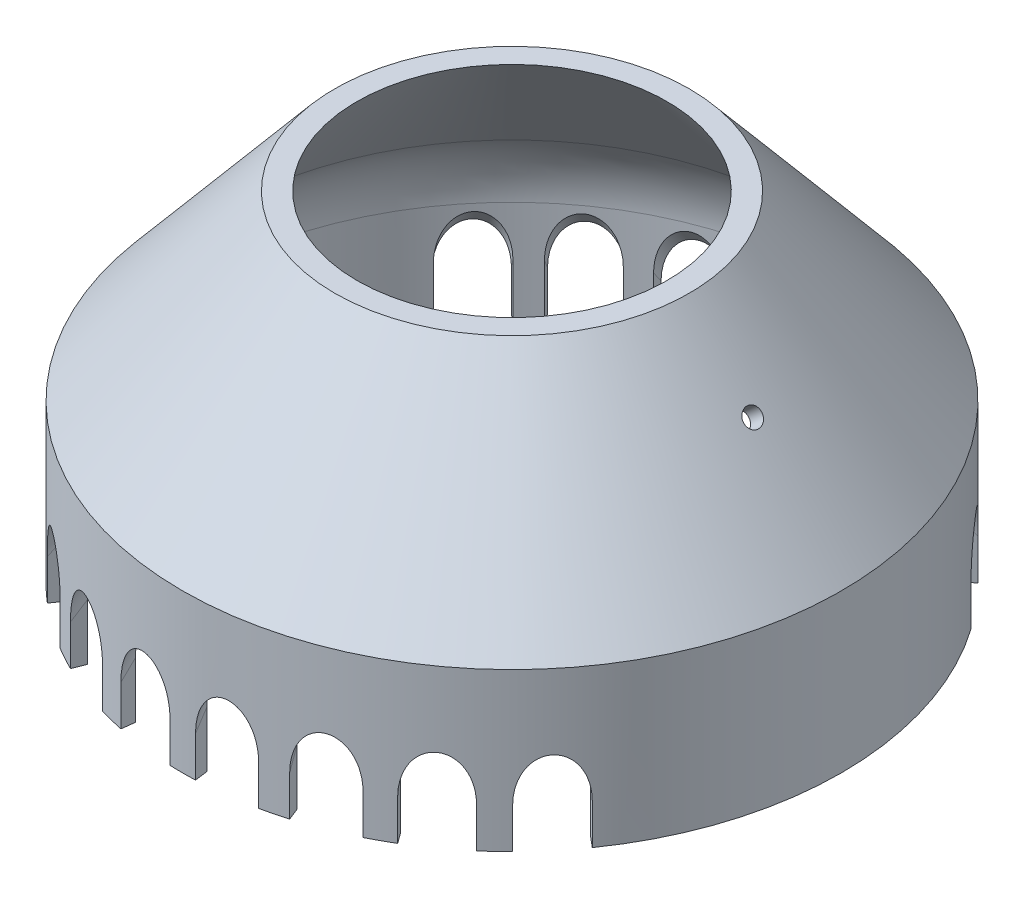
SolidWorks part; units mm, degrees
ref_plane "Front Plane" through (0, 0, 0) normal (0, 0, 1) x (1, 0, 0)
ref_plane "Top Plane" through (0, 0, 0) normal (0, 1, 0) x (1, 0, 0)
ref_plane "Right Plane" through (0, 0, 0) normal (1, 0, 0) x (0, 0, -1)
sketch "Cone Cross Section" plane through (0, 0, 0) normal (0, 0, -1) x (1, 0, 0)
  line L0 (0, 0) -> (13.7186, 0) construction
  line L1 (13.7186, 0) -> (25.6604, 14.2318)
  line L2 (28, 17.02) -> (29.1491, 16.0558) construction
  line L3 (13.7186, 0) -> (15.6767, 0)
  line L4 (29.1491, 16.0558) -> (15.6767, 0)
  line L5 (28, 20.6597) -> (28, 30)
  line L6 (0, 0) -> (0, 15.7221) construction
  line L7 (28, 30) -> (29.1491, 30)
  line L8 (29.1491, 30) -> (29.1491, 16.0558)
  arc A0 (25.6604, 14.2318) -> (28, 20.6597) centre (18, 20.6597) ccw
  dimension "D6" = 10
  dimension "D1" = 28
  dimension "D2" = 17.02
  dimension "D3" = 1.5
  dimension "D4" = 30
  dimension "D5" = 1.1491
  dimension "D7" = 13.9442
revolve "Revolve1" add sketch "Cone Cross Section" angle 360 about L6
sketch "Support Hole Plane Def Line" plane through (0, 0, 0) normal (0, 1, 0) x (1, 0, 0)
  line L0 (13.7186, 5) -> (13.7186, -5)
  line L1 (0, 0) -> (-13.7186, 0) construction
  line L3 (-13.7186, 5) -> (-13.7186, -5)
  line L4 (0, 0) -> (13.7186, 0) construction
  dimension "D1" = 10
ref_plane "Support Hole Plane 1" through (8.0504, 6.7551, 0) normal (-0.766, -0.6428, 0) x (0, 0, 1)
ref_plane "Support Hole Plane 2" through (-8.0504, 6.7551, 0) normal (0.766, -0.6428, 0) x (0, 0, -1)
sketch "Sketch3" plane through (8.0504, 6.7551, 0) normal (-0.766, -0.6428, 0) x (0, 0, 1)
  line L0 (0, -18.8181) -> (0, -8.8181) construction
  circle A0 centre (0, -18.8181) radius 0.8064
sketch "Sketch4" plane through (-8.0504, 6.7551, 0) normal (-0.766, 0.6428, 0) x (0, 0, 1)
  line L0 (0, -18.8181) -> (0, -8.8181) construction
  circle A0 centre (0, -18.8181) radius 0.8064
extrude "Support Hole 1" cut sketch "Sketch4" along normal up to next and the other way up to next
extrude "Support Hole 2" cut sketch "Sketch3" along normal up to next and the other way up to next
sketch "Sketch5" plane through (7.7889, -12.1174, 6.5357) normal (-0.4924, 0.766, -0.4132) x (0.8704, 0.4334, -0.2338)
  line L1 (3.5458, -3.8839) -> (1.4293, -5.8161) construction
  line L3 (4.9663, -7.6647) -> (6.0741, -6.6534) construction
  line L4 (1.6995, -5.5695) -> (-1.6717, -1.8769)
  line L5 (-1.6717, -1.8769) -> (2.0209, 1.4943)
  line L9 (2.0209, 1.4943) -> (5.3921, -2.1984)
  line L10 (7.1819, -5.642) -> (2.4623, -0.4724) construction
  arc A0 (1.6995, -5.5695) -> (5.3921, -2.1984) centre (3.5458, -3.8839) ccw
  dimension "D1" = 5
  dimension "D2" = 5
extrude "Turn Tool Channel" cut sketch "Sketch5" against normal up to next
ref_plane "Plane4" through (0, -10.826, 0) normal (0, -1, 0) x (-0.766, 0, -0.6428)
sketch "KeyPieceRotationArcCopy" plane through (0, -10.826, 0) normal (0, -1, 0) x (-0.766, 0, -0.6428)
  arc A0 (-11.7067, 0) -> (2.0328, -11.5288) centre (0, 0) ccw construction
  arc A1 (-11.7067, 0) -> (2.0328, -11.5288) centre (0, 0) ccw
pattern_curve "CrvPattern2" of "Turn Tool Channel" parameters "D1"=8, "D3"=50, "D2"=1, "D4"=50
ref_plane "Center Mirror Plane" through (0, 0, 0) normal (0, 0, 1) x (1, 0, 0)
mirror "Mirror1" about plane through (0, 0, 0) normal (0, 0, 1) of "Turn Tool Channel", "CrvPattern2"
equation "\"ConeAngle\"= \"KeyAngle@drive_circle_16_mcube.SLDPRT\""
equation "\"ConeBase\"= \"ConeBaseRadius@Outer Cone Spacer@drive_circle_16_mcube.SLDPRT\""
equation "\"ConeHoleHeight\"= \"ConeHoleHeight@drive_circle_16_mcube.SLDPRT\""
